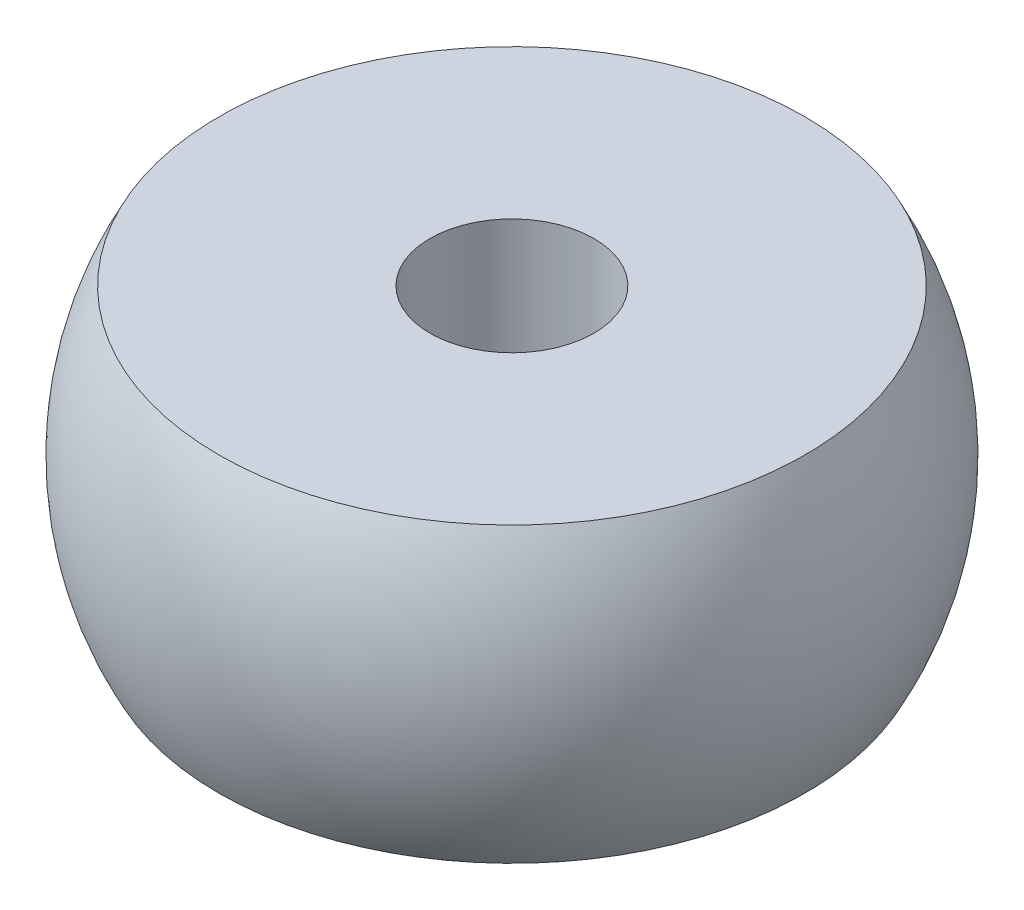
SolidWorks part; units mm, degrees
material "Nylon 101"
ref_plane "Front Plane" through (0, 0, 0) normal (0, 0, 1) x (1, 0, 0)
ref_plane "Top Plane" through (0, 0, 0) normal (0, 1, 0) x (1, 0, 0)
ref_plane "Right Plane" through (0, 0, 0) normal (1, 0, 0) x (0, 0, -1)
sketch "Sketch1" plane through (0, 0, 0) normal (0, 0, 1) x (1, 0, 0)
  line L0 (-1.778, 0) -> (0, 0) construction
  line L1 (-6.35, 3.175) -> (-1.778, 3.175)
  line L2 (-6.35, 3.175) -> (-6.35, -3.175) construction
  line L3 (-6.35, -3.175) -> (-1.778, -3.175)
  line L4 (-1.778, 3.175) -> (-1.778, -3.175)
  line L5 (0, 0) -> (0, 6.7463) construction
  arc A0 (-6.35, 3.175) -> (-6.35, -3.175) centre (-0.3969, 0) ccw
  dimension "D4" = 0.7937
  dimension "D1" = 3.556
  dimension "D2" = 6.35
  dimension "D3" = 6.35
revolve "Revolve1" add sketch "Sketch1" angle 360 about L5
